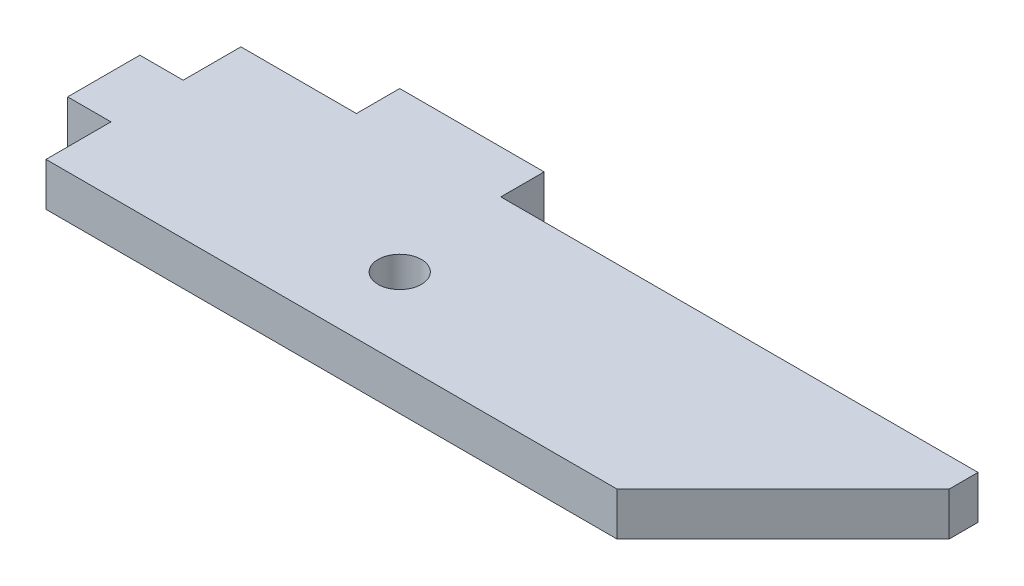
SolidWorks part; units mm, degrees
material "Acrylic (Medium-high impact)"
ref_plane "Front Plane" through (0, 0, 0) normal (0, 0, 1) x (1, 0, 0)
ref_plane "Top Plane" through (0, 0, 0) normal (0, 1, 0) x (1, 0, 0)
ref_plane "Right Plane" through (0, 0, 0) normal (1, 0, 0) x (0, 0, -1)
sketch "Sketch1" plane through (0, 0, 0) normal (0, 1, 0) x (1, 0, 0)
  line L0 (-47.38, 7.4134) -> (-47.38, 4.4134)
  line L1 (-47.38, 7.4134) -> (-37.38, 7.4134)
  line L2 (-4.33, 2.4034) -> (-15.82, -9.0866)
  line L3 (-15.82, -9.0866) -> (-55.38, -9.0866)
  line L4 (-37.38, 7.4134) -> (-37.38, 4.4134)
  line L5 (-37.38, 4.4134) -> (-4.33, 4.4134)
  line L6 (-47.38, 4.4134) -> (-55.38, 4.4134)
  line L7 (-55.38, 0.4134) -> (-58.38, 0.4134)
  line L8 (-58.38, 0.4134) -> (-58.38, -4.5866)
  line L9 (-55.38, -9.0866) -> (-55.38, -4.5866)
  line L10 (-58.38, -4.5866) -> (-55.38, -4.5866)
  line L11 (-55.38, 0.4134) -> (-55.38, 4.4134)
  line L12 (-4.33, 4.4134) -> (-4.33, 2.4034)
  circle A0 centre (-36.38, -3.5866) radius 1.5
  dimension "D8" = 3
  dimension "D1" = 10
  dimension "D2" = 8
  dimension "D3" = 3
  dimension "D4" = 13.5
  dimension "D5" = 135
  dimension "D6" = 4
  dimension "D7" = 54.05
  dimension "D9" = 5
  dimension "D10" = 8
  dimension "D11" = 22
  dimension "D12" = 39.56
extrude "Boss-Extrude1" add sketch "Sketch1" along normal blind 3
